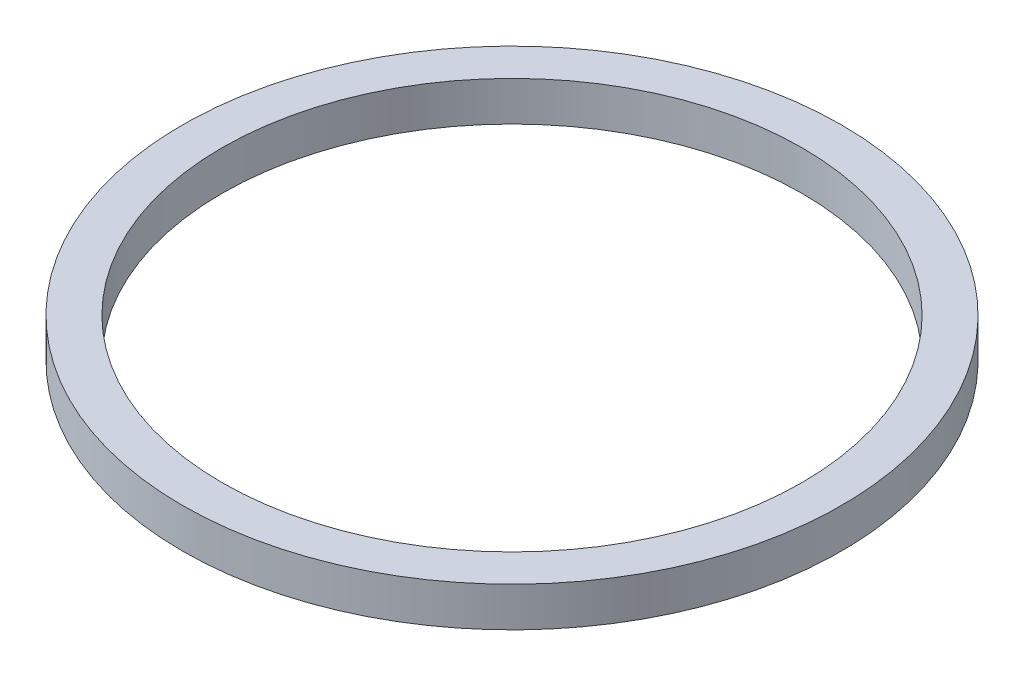
SolidWorks part; units mm, degrees
ref_plane "Front Plane" through (0, 0, 0) normal (0, 0, 1) x (1, 0, 0)
ref_plane "Top Plane" through (0, 0, 0) normal (0, 1, 0) x (1, 0, 0)
ref_plane "Right Plane" through (0, 0, 0) normal (1, 0, 0) x (0, 0, -1)
sketch "Sketch1" plane through (0, 0, 0) normal (0, 1, 0) x (1, 0, 0)
  circle A0 centre (0, 0) radius 25
  circle A1 centre (0, 0) radius 22
  dimension "D1" = 50
  dimension "D2" = 44
extrude "Boss-Extrude1" add sketch "Sketch1" along normal blind 3
